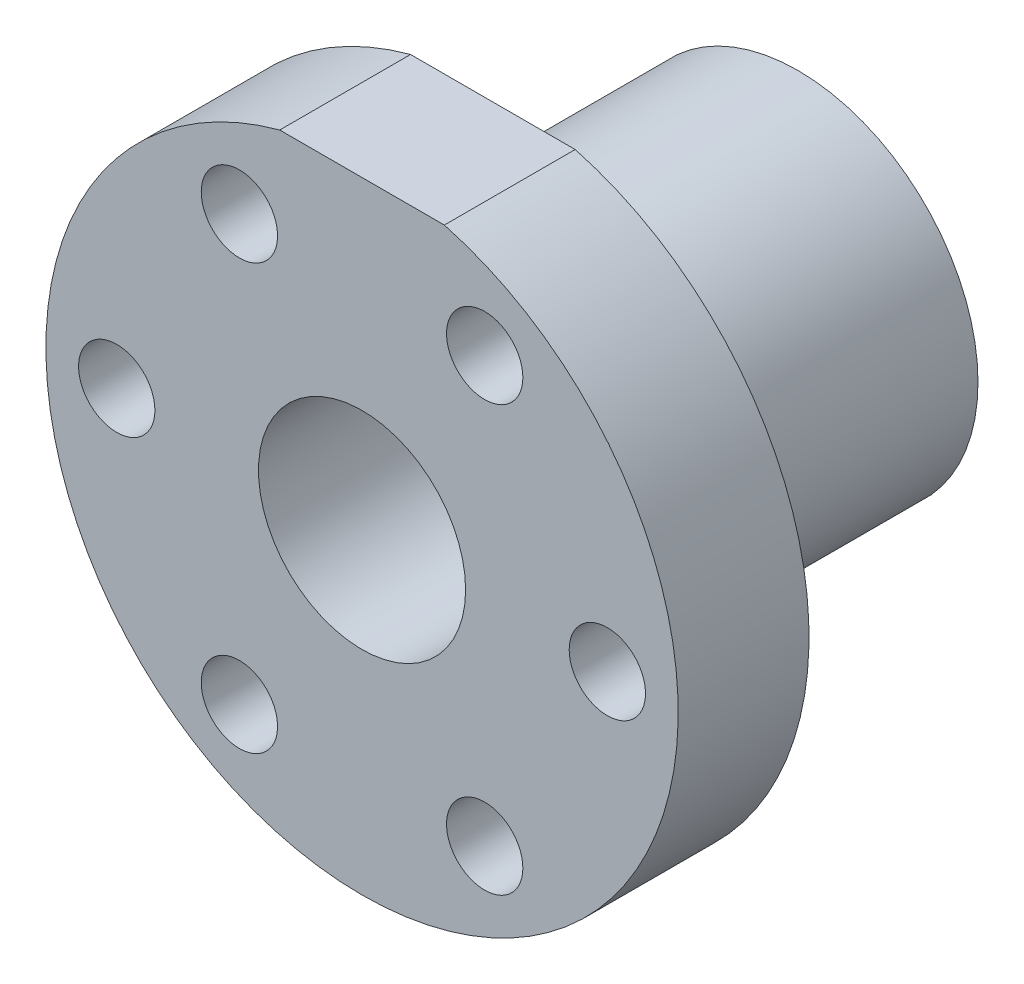
SolidWorks part; units mm, degrees
ref_plane "Płaszczyzna przednia" through (0, 0, 0) normal (0, 0, 1) x (1, 0, 0)
ref_plane "Płaszczyzna górna" through (0, 0, 0) normal (0, 1, 0) x (1, 0, 0)
ref_plane "Płaszczyzna prawa" through (0, 0, 0) normal (1, 0, 0) x (0, 0, -1)
sketch "Szkic1" plane through (0, 0, 0) normal (0, 0, 1) x (1, 0, 0)
  circle A0 centre (0, 0) radius 16.5
extrude "Dodanie-wyciągnięcie1" add sketch "Szkic1" along normal blind 28
sketch "Szkic2" plane through (0, 0, 28) normal (0, 0, 1) x (1, 0, 0)
  circle A0 centre (0, 0) radius 29
extrude "Dodanie-wyciągnięcie2" add sketch "Szkic2" along normal blind 12
sketch "Szkic3" plane through (0, 0, 40) normal (0, 0, 1) x (1, 0, 0)
  circle A0 centre (0, 0) radius 9.5
extrude "Wytnij-wyciągnięcie1" cut sketch "Szkic3" against normal blind 40
sketch "Szkic4" plane through (0, 0, 40) normal (0, 0, 1) x (1, 0, 0)
  line L1 (-17.4822, 29) -> (16.0048, 29)
  line L2 (-17.4822, 29) -> (-17.4822, 28)
  line L3 (-17.4822, 28) -> (16.0048, 28)
  line L4 (16.0048, 29) -> (16.0048, 28)
  circle A0 centre (0, 0) radius 29 construction
  dimension "D1" = 1
extrude "Wytnij-wyciągnięcie2" cut sketch "Szkic4" against normal blind 12
sketch "Szkic5" plane through (0, 0, 40) normal (0, 0, 1) x (1, 0, 0)
  circle A0 centre (-22.5, 0) radius 3.5
  arc A1 (-7.5498, 28) -> (7.5498, 28) centre (0, 0) ccw construction
  dimension "D1" = 22.5
extrude "Wytnij-wyciągnięcie3" cut sketch "Szkic5" against normal blind 12
pattern_circular "Szyk kołowy1" count 6 every 60 about axis through (0, 0, 0) along (0, 0, 1) of "Wytnij-wyciągnięcie3"
